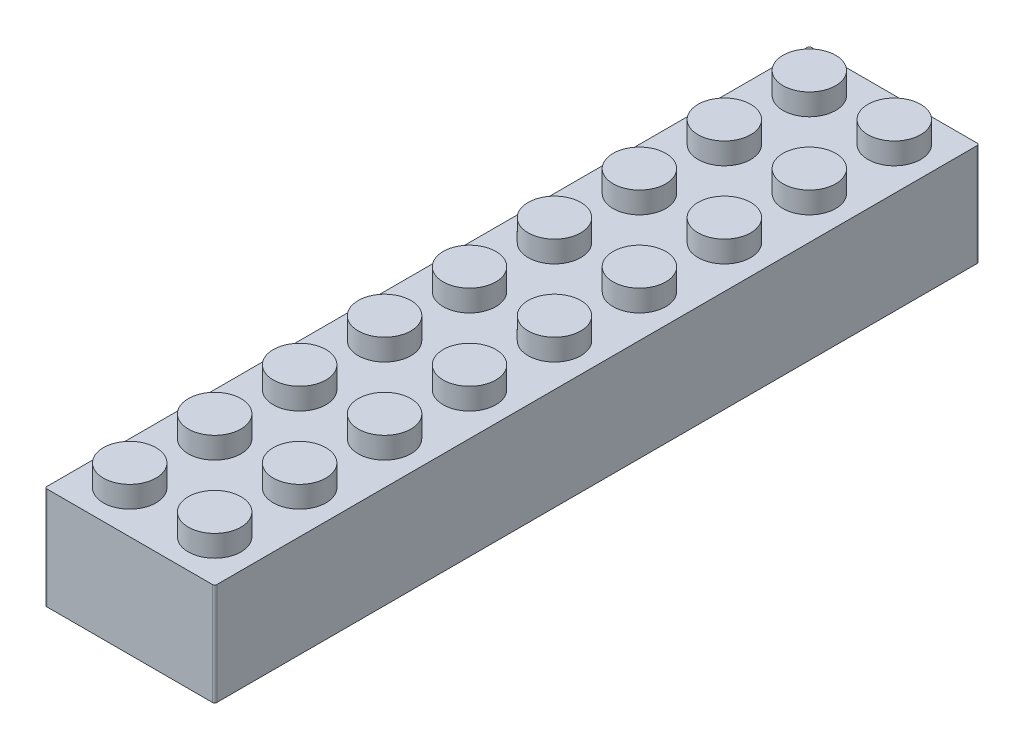
SolidWorks part; units mm, degrees
ref_plane "Front Plane" through (0, 0, 0) normal (0, 0, 1) x (1, 0, 0)
ref_plane "Top Plane" through (0, 0, 0) normal (0, 1, 0) x (1, 0, 0)
ref_plane "Right Plane" through (0, 0, 0) normal (1, 0, 0) x (0, 0, -1)
sketch "stencil" plane through (0, 0, 0) normal (0, 1, 0) x (1, 0, 0)
  line L2 (7.9, 71.1) -> (7.9, 0) construction
  line L29 (14.3, 1.5) -> (1.5, 1.5)
  line L30 (15.8, 71.1) -> (0, 71.1)
  line L32 (15.8, 71.1) -> (15.8, 0)
  line L34 (15.8, 0) -> (0, 0)
  line L36 (0, 71.1) -> (0, 0)
  line L37 (7.9, 0) -> (7.9, 71.1) construction
  line L38 (15.8, 35.55) -> (0, 35.55) construction
  line L39 (1.5, 69.6) -> (1.5, 1.5)
  line L40 (14.3, 69.6) -> (1.5, 69.6)
  line L41 (14.3, 69.6) -> (14.3, 1.5)
  circle A40 centre (3.95, 3.95) radius 2.45
  circle A41 centre (7.9, 7.9) radius 3.25
  circle A42 centre (3.95, 11.85) radius 2.45
  circle A43 centre (3.95, 19.75) radius 2.45
  circle A44 centre (3.95, 27.65) radius 2.45
  circle A45 centre (7.9, 15.8) radius 3.25
  circle A46 centre (7.9, 23.7) radius 3.25
  circle A47 centre (7.9, 31.6) radius 3.25
  circle A48 centre (3.95, 35.55) radius 2.45
  circle A49 centre (3.95, 43.45) radius 2.45
  circle A50 centre (3.95, 51.35) radius 2.45
  circle A51 centre (7.9, 39.5) radius 3.25
  circle A52 centre (7.9, 47.4) radius 3.25
  circle A53 centre (3.95, 59.25) radius 2.45
  circle A54 centre (3.95, 67.15) radius 2.45
  circle A55 centre (7.9, 55.3) radius 3.25
  circle A56 centre (7.9, 63.2) radius 3.25
  circle A57 centre (7.9, 7.9) radius 2.45
  circle A58 centre (7.9, 15.8) radius 2.45
  circle A59 centre (7.9, 23.7) radius 2.45
  circle A60 centre (7.9, 31.6) radius 2.45
  circle A61 centre (7.9, 39.5) radius 2.45
  circle A62 centre (7.9, 47.4) radius 2.45
  circle A63 centre (7.9, 55.3) radius 2.45
  circle A64 centre (7.9, 63.2) radius 2.45
  circle A65 centre (11.85, 11.85) radius 2.45
  circle A66 centre (11.85, 19.75) radius 2.45
  circle A67 centre (11.85, 27.65) radius 2.45
  circle A68 centre (11.85, 35.55) radius 2.45
  circle A69 centre (11.85, 43.45) radius 2.45
  circle A70 centre (11.85, 51.35) radius 2.45
  circle A71 centre (11.85, 59.25) radius 2.45
  circle A72 centre (11.85, 67.15) radius 2.45
  circle A73 centre (11.85, 3.95) radius 2.45
  point P1 (0, 0)
  point P6 (3.95, -15.8)
  point P9 (7.9, -15.8)
  point P10 (7.9, -11.85)
  point P13 (3.95, -7.9)
  point P15 (7.9, -7.9)
  point P17 (7.9, -3.95)
  point P18 (3.95, 0)
  point P21 (7.9, 0)
  point P25 (7.9, 3.95)
  point P27 (3.95, 7.9)
  point P28 (7.9, 7.9)
  point P29 (0, -11.85)
  point P30 (0, -7.9)
  point P31 (0, 3.95)
  point P34 (0, -3.95)
  point P35 (3.95, 0)
  point P36 (0, 15.8)
  point P37 (0, 23.7)
  point P38 (7.9, 23.7)
  point P39 (15.8, 23.7)
  point P40 (15.8, 15.8)
  point P41 (15.8, 7.9)
  point P43 (7.9, 0)
  point P48 (11.85, 0)
  point P49 (15.8, 0)
  point P50 (3.95, 3.95)
  point P51 (7.9, 3.95)
  point P52 (11.85, 3.95)
  point P53 (15.8, 3.95)
  point P54 (3.95, 7.9)
  point P55 (7.9, 7.9)
  point P56 (11.85, 7.9)
  point P57 (15.8, 7.9)
  point P58 (3.95, 11.85)
  point P59 (7.9, 11.85)
  point P60 (11.85, 11.85)
  point P61 (15.8, 11.85)
  point P63 (3.95, 15.8)
  point P64 (7.9, 15.8)
  point P65 (11.85, 15.8)
  point P66 (15.8, 15.8)
  point P67 (3.95, 19.75)
  point P68 (7.9, 19.75)
  point P69 (11.85, 19.75)
  point P70 (15.8, 19.75)
  point P71 (3.95, 23.7)
  point P72 (7.9, 23.7)
  point P73 (11.85, 23.7)
  point P75 (15.8, 23.7)
  point P77 (3.95, 27.65)
  point P79 (7.9, 27.65)
  point P81 (11.85, 27.65)
  point P83 (15.8, 27.65)
  point P85 (3.95, 31.6)
  point P87 (7.9, 31.6)
  point P88 (11.85, 31.6)
  point P89 (15.8, 31.6)
  point P90 (0, 3.95)
  point P91 (0, 7.9)
  point P92 (0, 11.85)
  point P93 (0, 15.8)
  point P94 (0, 19.75)
  point P95 (0, 23.7)
  point P96 (0, 27.65)
  point P97 (0, 31.6)
  point P113 (0, 35.55)
  point P114 (3.95, 35.55)
  point P115 (7.9, 35.55)
  point P116 (11.85, 35.55)
  point P117 (15.8, 35.55)
  point P118 (0, 39.5)
  point P119 (3.95, 39.5)
  point P120 (7.9, 39.5)
  point P121 (11.85, 39.5)
  point P122 (15.8, 39.5)
  point P124 (0, 43.45)
  point P125 (3.95, 43.45)
  point P126 (7.9, 43.45)
  point P127 (11.85, 43.45)
  point P128 (15.8, 43.45)
  point P129 (0, 47.4)
  point P130 (3.95, 47.4)
  point P131 (7.9, 47.4)
  point P132 (11.85, 47.4)
  point P133 (15.8, 47.4)
  point P135 (0, 51.35)
  point P136 (3.95, 51.35)
  point P137 (7.9, 51.35)
  point P138 (11.85, 51.35)
  point P139 (15.8, 51.35)
  point P140 (0, 55.3)
  point P141 (3.95, 55.3)
  point P142 (7.9, 55.3)
  point P143 (11.85, 55.3)
  point P144 (15.8, 55.3)
  point P145 (0, 59.25)
  point P146 (3.95, 59.25)
  point P147 (7.9, 59.25)
  point P148 (11.85, 59.25)
  point P149 (15.8, 59.25)
  point P150 (0, 63.2)
  point P151 (3.95, 63.2)
  point P152 (7.9, 63.2)
  point P153 (11.85, 63.2)
  point P154 (15.8, 63.2)
  point P165 (0, 67.15)
  point P166 (3.95, 67.15)
  point P167 (7.9, 67.15)
  point P168 (11.85, 67.15)
  point P169 (15.8, 67.15)
  point P170 (0, 71.1)
  point P171 (3.95, 71.1)
  point P172 (7.9, 71.1)
  point P173 (11.85, 71.1)
  point P174 (15.8, 71.1)
  point P182 (7.9, 35.55)
  dimension "D8" = 4.9
  dimension "D9" = 6.5
  dimension "D3" = 3.95
  dimension "D4" = 3.95
  dimension "D5" = 15.8
  dimension "D6" = 71.1
  dimension "D7" = 0.8
  dimension "D10" = 1.5
  dimension "D1" = 5
sketch "Sketch1" plane through (0, 0, 0) normal (0, 1, 0) x (1, 0, 0)
  line L1 (15.8, 71.1) -> (0, 71.1)
  line L2 (15.8, 71.1) -> (15.8, 0)
  line L3 (15.8, 0) -> (0, 0)
  line L4 (0, 71.1) -> (0, 0)
  line L5 (7.9, 0) -> (7.9, 71.1) construction
  line L6 (15.8, 35.55) -> (0, 35.55) construction
  point P0 (7.9, 35.55)
extrude "Boss-Extrude1" add sketch "Sketch1" along normal mid plane 9.5
sketch "Sketch2" plane through (0, 4.75, 0) normal (0, 1, 0) x (1, 0, 0)
  line L0 (0, 71.1) -> (0, 0) construction
  circle A0 centre (3.95, 3.95) radius 2.45
  circle A1 centre (11.85, 3.95) radius 2.45
  circle A2 centre (11.85, 11.85) radius 2.45
  circle A3 centre (3.95, 11.85) radius 2.45
  circle A4 centre (3.95, 19.75) radius 2.45
  circle A5 centre (3.95, 27.65) radius 2.45
  circle A6 centre (11.85, 27.65) radius 2.45
  circle A7 centre (11.85, 35.55) radius 2.45
  circle A8 centre (3.95, 35.55) radius 2.45
  circle A9 centre (3.95, 43.45) radius 2.45
  circle A10 centre (11.85, 43.45) radius 2.45
  circle A11 centre (3.95, 51.35) radius 2.45
  circle A12 centre (11.85, 51.35) radius 2.45
  circle A13 centre (3.95, 59.25) radius 2.45
  circle A14 centre (11.85, 59.25) radius 2.45
  circle A15 centre (3.95, 67.15) radius 2.45
  circle A16 centre (11.85, 67.15) radius 2.45
  circle A17 centre (3.95, 3.95) radius 2.45 construction
  circle A18 centre (11.85, 19.75) radius 2.45
  circle A19 centre (11.85, 19.75) radius 2.45 construction
extrude "Boss-Extrude2" add sketch "Sketch2" along normal blind 2
sketch "Sketch3" plane through (0, -4.75, 0) normal (0, -1, 0) x (1, 0, 0)
  line L1 (14.3, -1.5) -> (1.5, -1.5)
  line L2 (14.3, -1.5) -> (14.3, -69.6)
  line L3 (14.3, -69.6) -> (1.5, -69.6)
  line L4 (1.5, -1.5) -> (1.5, -69.6)
  line L5 (7.9, -69.6) -> (7.9, -1.5) construction
  line L6 (14.3, -35.55) -> (1.5, -35.55) construction
  point P0 (7.9, -35.55)
extrude "Cut-Extrude1" cut sketch "Sketch3" against normal blind 4
sketch "Sketch4" plane through (0, -0.75, 0) normal (0, -1, 0) x (1, 0, 0)
  circle A0 centre (7.9, -63.2) radius 3.25
  circle A1 centre (7.9, -55.3) radius 3.25
  circle A2 centre (7.9, -47.4) radius 3.25
  circle A3 centre (7.9, -39.5) radius 3.25
  circle A4 centre (7.9, -31.6) radius 3.25
  circle A5 centre (7.9, -23.7) radius 3.25
  circle A6 centre (7.9, -15.8) radius 3.25
  circle A7 centre (7.9, -7.9) radius 3.25
  circle A8 centre (7.9, -7.9) radius 2.45
  circle A10 centre (7.9, -15.8) radius 2.45
  circle A11 centre (7.9, -23.7) radius 2.45
  circle A12 centre (7.9, -31.6) radius 2.45
  circle A13 centre (7.9, -39.5) radius 2.45
  circle A14 centre (7.9, -47.4) radius 2.45
  circle A15 centre (7.9, -55.3) radius 2.45
  circle A16 centre (7.9, -63.2) radius 2.45
  circle A17 centre (7.9, -63.2) radius 2.45 construction
  circle A18 centre (7.9, -63.2) radius 3.25 construction
extrude "Boss-Extrude3" add sketch "Sketch4" along normal up to surface (4 mm away) up to face at (7.9, -4.75, -35.55)
fillet "Fillet1" radius 0.2 4 edges at (0, 0, -71.1) (15.8, 0, -71.1) (0, 0, 0) (15.8, 0, 0)
equation "\"t\"= 0'tolerance"
equation "\"D5@stencil\"=15.80-\"t\""
equation "\"D10@stencil\"=1.5-\"t\""
equation "\"D6@stencil\"=71.10mm-\"t\""
equation "\"D9@stencil\"=6.50-\"t\""
equation "\"D1@Boss-Extrude1\"=9.5-\"t\""
